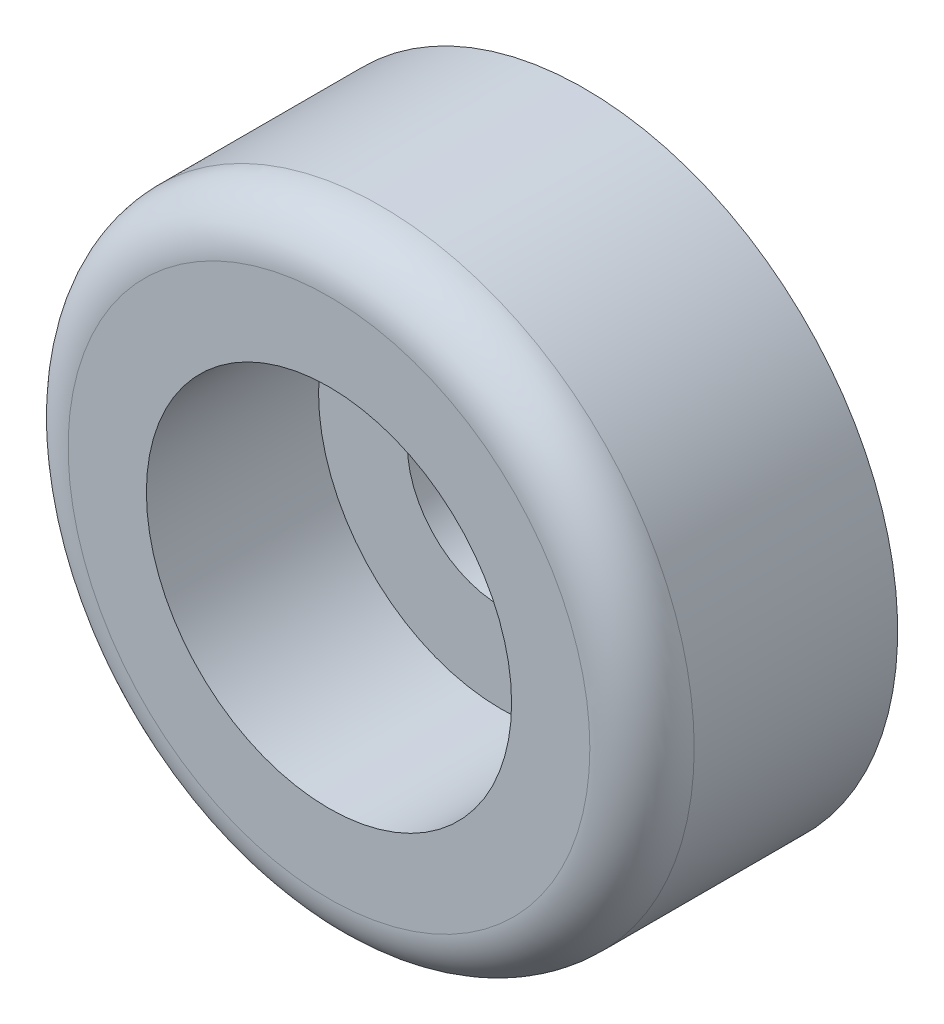
SolidWorks part; units mm, degrees
material "ABS"
ref_plane "Front" through (0, 0, 0) normal (0, 0, 1) x (1, 0, 0)
ref_plane "Top" through (0, 0, 0) normal (0, 1, 0) x (1, 0, 0)
ref_plane "Right" through (0, 0, 0) normal (1, 0, 0) x (0, 0, -1)
sketch "Croquis1" plane through (0, 0, 0) normal (1, 0, 0) x (0, 0, -1)
  line L0 (0, 0) -> (-8.3234, 0) construction
  line L1 (0, 1.8) -> (0, 6)
  line L2 (0, 6) -> (-4.9, 6)
  line L3 (-4.9, 6) -> (-4.9, 3.5)
  line L4 (-4.9, 3.5) -> (-1.6, 3.5)
  line L5 (-1.6, 3.5) -> (-1.6, 1.8)
  line L6 (-1.6, 1.8) -> (0, 1.8)
  dimension "D1" = 3.6
  dimension "D2" = 12
  dimension "D3" = 7
  dimension "D4" = 1.6
  dimension "D5" = 4.9
revolve "Revolución1" add sketch "Croquis1" angle 360 about L0
fillet "Redondeo1" radius 1 1 edges at (-6, 0, 4.9)
